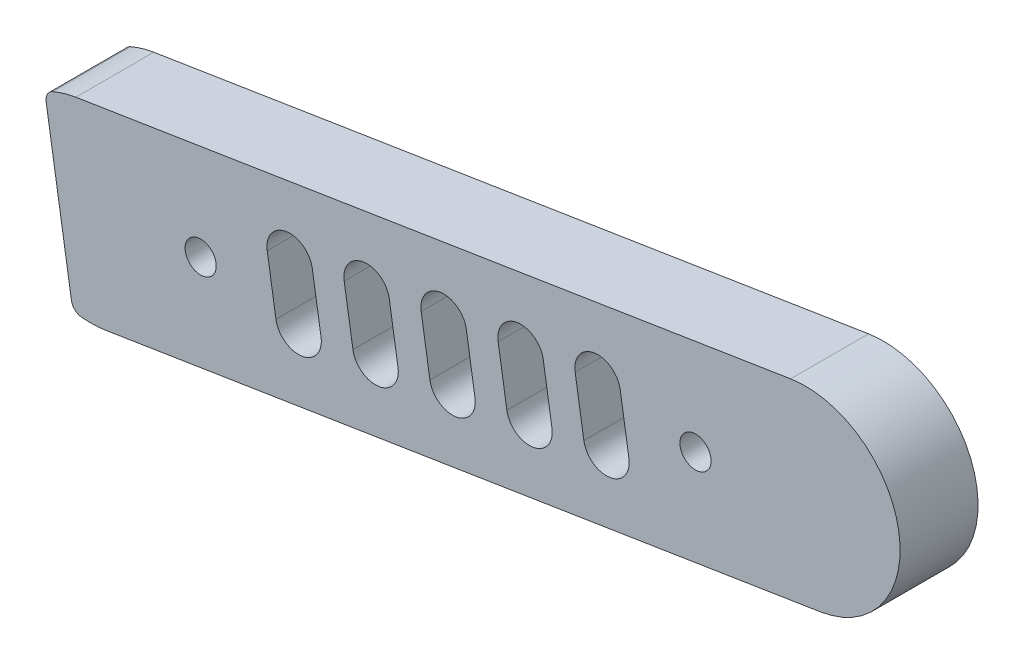
SolidWorks part; units mm, degrees
material "二氧化硅"
ref_plane "前视基准面" through (0, 0, 0) normal (0, 0, 1) x (1, 0, 0)
ref_plane "上视基准面" through (0, 0, 0) normal (0, 1, 0) x (1, 0, 0)
ref_plane "右视基准面" through (0, 0, 0) normal (1, 0, 0) x (0, 0, -1)
sketch "草图1" plane through (0, 0, 0) normal (0, 0, 1) x (1, 0, 0)
  line L0 (-42.0561, 57.6175) -> (22.1396, 67.811)
  line L1 (13.5963, 57.848) -> (-30.8469, 50.7909) construction
  line L2 (-2.1039, 57.8863) -> (-1.3198, 52.9482) construction
  line L3 (10.485, 48.7475) -> (24.8056, 51.0214) construction
  line L4 (24.8056, 51.0214) -> (-39.3901, 40.8279)
  line L5 (-44.7251, 55.9335) -> (-42.4495, 41.6024)
  line L6 (4.8094, 58.9841) -> (5.5936, 54.0459) construction
  line L7 (6.8341, 59.3055) -> (7.6182, 54.3674)
  line L8 (2.7848, 58.6626) -> (3.5689, 53.7244)
  line L9 (-0.0793, 58.2078) -> (0.7048, 53.2697)
  line L10 (2.7848, 58.6626) -> (3.5689, 53.7244) construction
  line L11 (-4.1286, 57.5648) -> (-3.3445, 52.6267)
  line L12 (-9.0173, 56.7885) -> (-8.2332, 51.8504) construction
  line L13 (-6.9927, 57.11) -> (-6.2086, 52.1719)
  line L14 (-11.042, 56.467) -> (-10.2578, 51.5289)
  line L15 (-15.9307, 55.6908) -> (-15.1466, 50.7526) construction
  line L16 (-13.9061, 56.0123) -> (-13.122, 51.0741)
  line L17 (-17.9554, 55.3693) -> (-17.1712, 50.4312)
  line L18 (-22.8441, 54.593) -> (-22.06, 49.6549) construction
  line L19 (-20.8195, 54.9145) -> (-20.0354, 49.9764)
  line L20 (-24.8687, 54.2715) -> (-24.0846, 49.3334)
  arc A0 (22.1396, 67.811) -> (24.8056, 51.0214) centre (23.4726, 59.4162) cw
  arc A1 (24.8056, 51.0214) -> (22.1396, 67.811) centre (23.4726, 59.4162) ccw construction
  arc A2 (-39.3901, 40.8279) -> (-41.5603, 40.764) centre (-40.7231, 49.2227) cw
  arc A3 (-42.0561, 57.6175) -> (-44.1393, 57.006) centre (-40.7231, 49.2227) ccw
  arc A4 (-44.1393, 57.006) -> (-44.7251, 55.9335) centre (-43.7374, 56.0903) ccw
  arc A5 (-41.5603, 40.764) -> (-42.4495, 41.6024) centre (-41.4618, 41.7592) cw
  circle A6 centre (-30.8469, 50.7909) radius 1.4
  circle A7 centre (13.5963, 57.848) radius 1.4
  arc A8 (6.8341, 59.3055) -> (2.7848, 58.6626) centre (4.8094, 58.9841) ccw
  arc A9 (3.5689, 53.7244) -> (7.6182, 54.3674) centre (5.5936, 54.0459) ccw
  arc A10 (-0.0793, 58.2078) -> (-4.1286, 57.5648) centre (-2.1039, 57.8863) ccw
  arc A11 (-3.3445, 52.6267) -> (0.7048, 53.2697) centre (-1.3198, 52.9482) ccw
  arc A12 (-6.9927, 57.11) -> (-11.042, 56.467) centre (-9.0173, 56.7885) ccw
  arc A13 (-10.2578, 51.5289) -> (-6.2086, 52.1719) centre (-8.2332, 51.8504) ccw
  arc A14 (-13.9061, 56.0123) -> (-17.9554, 55.3693) centre (-15.9307, 55.6908) ccw
  arc A15 (-17.1712, 50.4312) -> (-13.122, 51.0741) centre (-15.1466, 50.7526) ccw
  arc A16 (-20.8195, 54.9145) -> (-24.8687, 54.2715) centre (-22.8441, 54.593) ccw
  arc A17 (-24.0846, 49.3334) -> (-20.0354, 49.9764) centre (-22.06, 49.6549) ccw
  point P34 (5.2015, 56.515)
  point P45 (-1.7119, 55.4172)
  point P54 (-8.6253, 54.3195)
  point P61 (-15.5387, 53.2217)
  point P68 (-22.452, 52.1239)
  dimension "D1" = 5
extrude "凸台-拉伸1" add sketch "草图1" along normal blind 7
